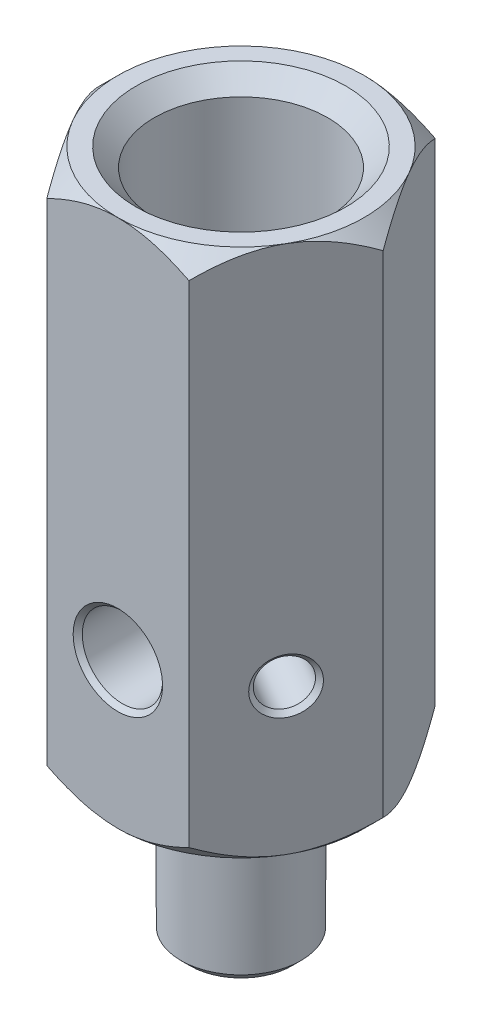
SolidWorks part; units mm, degrees
material "7075-T6 (SN)"
ref_plane "Front Plane" through (0, 0, 0) normal (0, 0, 1) x (1, 0, 0)
ref_plane "Top Plane" through (0, 0, 0) normal (0, 1, 0) x (1, 0, 0)
ref_plane "Right Plane" through (0, 0, 0) normal (1, 0, 0) x (0, 0, -1)
sketch "Sketch1" plane through (0, 0, 0) normal (0, 1, 0) x (1, 0, 0)
  line L1 (7.7942, -13.5) -> (15.5885, 0)
  line L2 (15.5885, 0) -> (7.7942, 13.5)
  line L3 (7.7942, 13.5) -> (-7.7942, 13.5)
  line L4 (-7.7942, 13.5) -> (-15.5885, 0)
  line L5 (-15.5885, 0) -> (-7.7942, -13.5)
  line L6 (-7.7942, -13.5) -> (7.7942, -13.5)
  circle A0 centre (0, 0) radius 13.5 construction
  dimension "D1" = 27
extrude "Boss-Extrude1" add sketch "Sketch1" along normal blind 75
sketch "Sketch2" plane through (0, 0, 0) normal (0, -1, 0) x (1, 0, 0)
  circle A0 centre (0, 0) radius 6.58
  line M2 (7.7942, 13.5) -> (-7.7942, 13.5)
  line M3 (-7.7942, 13.5) -> (-15.5885, 0)
  line M4 (-15.5885, 0) -> (-7.7942, -13.5)
  line M5 (-7.7942, -13.5) -> (7.7942, -13.5)
  line M6 (7.7942, -13.5) -> (15.5885, 0)
  line M7 (15.5885, 0) -> (7.7942, 13.5)
  dimension "D1" = 13.16
extrude "Cut-Extrude1" cut sketch "Sketch2" against normal blind 15 contours A0 M7 M2 M3 M4 M5 M6
sketch "Sketch3" plane through (0, 15, 0) normal (0, -1, 0) x (1, 0, 0)
  circle A0 centre (0, 0) radius 5.5
  dimension "D1" = 11
extrude "Cut-Extrude3" cut sketch "Sketch3" against normal blind 2 flip side to cut contours A0
sketch "Sketch4" plane through (0, 0, 0) normal (0, -1, 0) x (1, 0, 0)
  circle A0 centre (0, 0) radius 3.4
  dimension "D1" = 6.8
extrude "Cut-Extrude4" cut sketch "Sketch4" against normal through all
sketch "Sketch5" plane through (0, 75, 0) normal (0, 1, 0) x (1, 0, 0)
  circle A0 centre (0, 0) radius 5.9
  dimension "D1" = 11.8
extrude "Cut-Extrude5" cut sketch "Sketch5" against normal blind 36
sketch "Sketch7" plane through (0, 75, 0) normal (0, 1, 0) x (1, 0, 0)
  circle A0 centre (0, 0) radius 9.5
  dimension "D1" = 19
extrude "Cut-Extrude7" cut sketch "Sketch7" against normal blind 19
sketch "Sketch8" plane through (0, 0, 13.5) normal (0, 0, 1) x (1, 0, 0)
  line L1 (-7.7942, 75) -> (7.7942, 75) construction
  circle A0 centre (0, 33) radius 4.4
  dimension "D1" = 8.8
  dimension "D2" = 42
extrude "Cut-Extrude8" cut sketch "Sketch8" against normal through all
sketch "Sketch9" plane through (-11.6913, 0, -6.75) normal (-0.866, 0, -0.5) x (-0.5, 0, 0.866)
  line L1 (-7.7942, 75) -> (7.7942, 75) construction
  circle A0 centre (0, 33) radius 2.5
  dimension "D1" = 5
  dimension "D2" = 42
extrude "Cut-Extrude9" cut sketch "Sketch9" against normal through all
sketch "Sketch10" plane through (0, 0, 0) normal (1, 0, 0) x (0, 0, -1)
  line L0 (8.5185, 79.9815) -> (18.4815, 70.0185)
  line L1 (18.4815, 70.0185) -> (18.4815, 79.9815)
  line L2 (18.4815, 79.9815) -> (8.5185, 79.9815)
  line L3 (16.2791, 19.7791) -> (10.7209, 14.2209)
  line L4 (10.7209, 14.2209) -> (16.2791, 14.2209)
  line L5 (16.2791, 14.2209) -> (16.2791, 19.7791)
  line L6 (0, 77.9815) -> (0, 74.4955) construction
revolve "Cut-Revolve1" cut sketch "Sketch10" angle 360 about L6
chamfer "Chamfer2" distance 0.5 angle 45 7 edges at (0, 56, 5.9) (4.4, 33, 13.5) (10.4413, 33, 8.9151) (4.4, 33, -13.5) (-12.9413, 33, -4.5849) (0, 39, 3.4) (0, 0, -3.4)
chamfer "Chamfer3" distance 2 angle 45 1 edges at (0, 75, 9.5)
chamfer "Chamfer4" distance 1 angle 45 2 edges at (0, 0, -6.58) (0, 15, -6.58)
